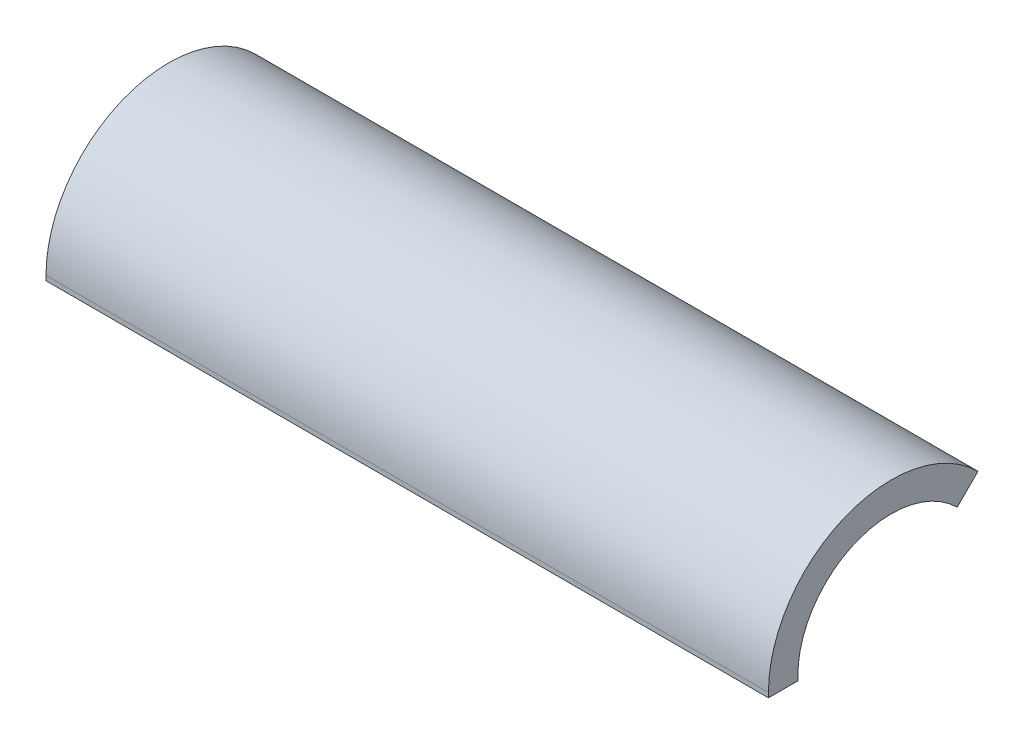
SolidWorks part; units mm, degrees
ref_plane "Front" through (0, 0, 0) normal (0, 0, 1) x (1, 0, 0)
ref_plane "Top" through (0, 0, 0) normal (0, 1, 0) x (1, 0, 0)
ref_plane "Right" through (0, 0, 0) normal (1, 0, 0) x (0, 0, -1)
sketch "Sketch1" plane through (0, 0, 0) normal (1, 0, 0) x (0, 0, -1)
  line L0 (0, 0) -> (-16.7005, 0) construction
  line L1 (0, 0) -> (11.809, 11.809) construction
  line L2 (-16.7005, 0) -> (-12.7, 0)
  line L3 (11.809, 11.809) -> (8.9803, 8.9803)
  arc A0 (8.9803, 8.9803) -> (-12.7, 0) centre (0, 0) ccw
  arc A1 (11.809, 11.809) -> (-16.7005, 0) centre (0, 0) ccw
  dimension "D1" = 25.4
  dimension "D2" = 33.401
  dimension "D3" = 135
extrude "Boss-Extrude1" add sketch "Sketch1" along normal blind 98.298
sketch "Sketch2" plane through (0, 0, 0) normal (0, -1, 0) x (1, 0, 0)
  line L1 (0, 12.7) -> (98.298, 12.7)
  line L2 (0, 12.7) -> (0, 16.7005)
  line L3 (0, 16.7005) -> (98.298, 16.7005)
  line L4 (98.298, 12.7) -> (98.298, 16.7005)
extrude "Boss-Extrude2" add sketch "Sketch2" along normal blind 0.635
